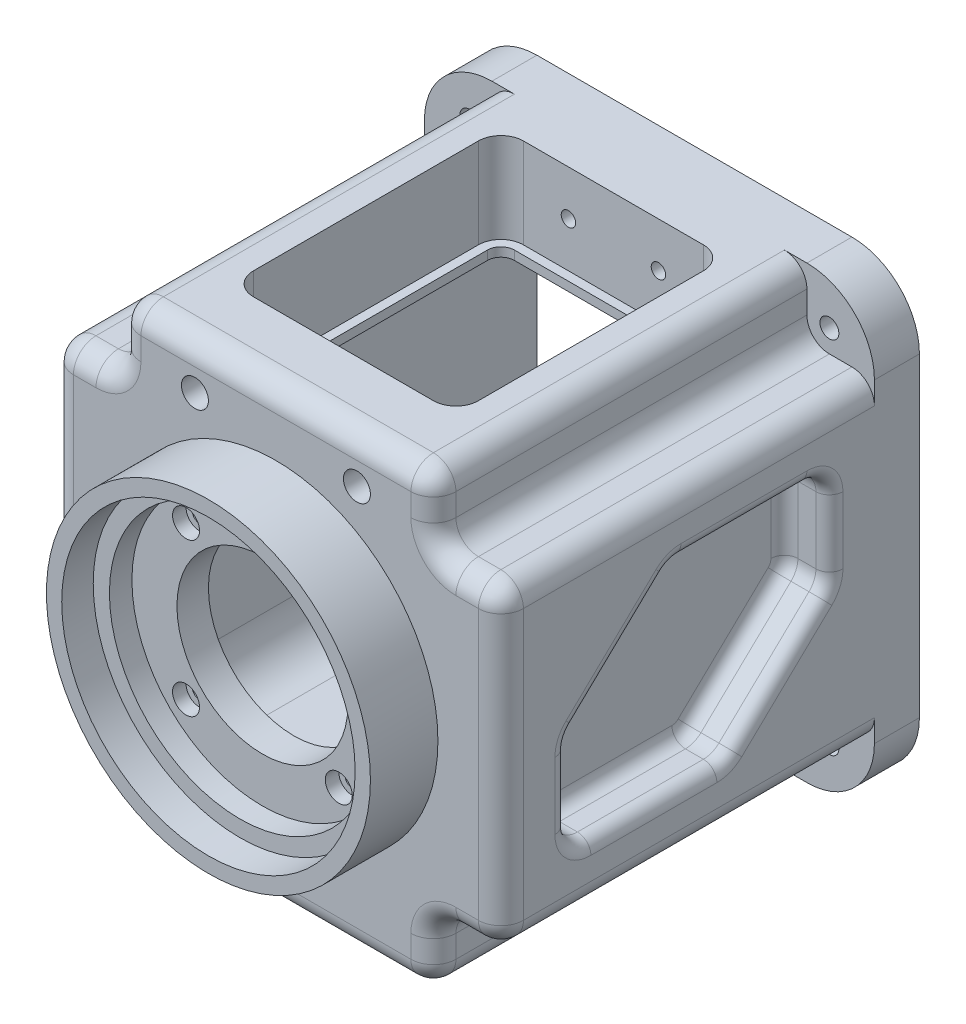
SolidWorks part; units mm, degrees
ref_plane "前视基准面" through (0, 0, 0) normal (0, 0, 1) x (1, 0, 0)
ref_plane "上视基准面" through (0, 0, 0) normal (0, 1, 0) x (1, 0, 0)
ref_plane "右视基准面" through (0, 0, 0) normal (1, 0, 0) x (0, 0, -1)
sketch "草图1" plane through (0, 0, 0) normal (0, 0, 1) x (1, 0, 0)
  line L1 (-50, 50) -> (50, 50)
  line L2 (-50, 50) -> (-50, -50)
  line L3 (-50, -50) -> (50, -50)
  line L4 (50, 50) -> (50, -50)
  line L5 (0, -50) -> (0, 50) construction
  line L6 (-50, 0) -> (50, 0) construction
  point P0 (0, 0)
  dimension "D1" = 100
  dimension "D2" = 100
extrude "凸台-拉伸1" add sketch "草图1" along normal blind 93
fillet "圆角1" radius 15 4 edges at (-50, -50, 46.5) (50, -50, 46.5) (50, 50, 46.5) (-50, 50, 46.5)
sketch "草图2" plane through (0, 0, 93) normal (0, 0, 1) x (1, 0, 0)
  line L0 (35, 50) -> (-35, 50) construction
  line L1 (-35, 50) -> (-50, 50)
  line L2 (-35, 50) -> (-35, 40)
  line L3 (-40, 35) -> (-50, 35)
  line L4 (-50, 50) -> (-50, 35)
  line L5 (-50, 35) -> (-50, -35) construction
  line L6 (50, 35) -> (40, 35)
  line L7 (50, 35) -> (50, 50)
  line L8 (50, 50) -> (35, 50)
  line L9 (35, 40) -> (35, 50)
  line L10 (35, -50) -> (35, -40)
  line L11 (35, -50) -> (50, -50)
  line L12 (50, -50) -> (50, -35)
  line L13 (40, -35) -> (50, -35)
  line L14 (-50, -35) -> (-40, -35)
  line L15 (-50, -35) -> (-50, -50)
  line L16 (-50, -50) -> (-35, -50)
  line L17 (-35, -40) -> (-35, -50)
  arc A0 (-35, 40) -> (-40, 35) centre (-40, 40) cw
  arc A1 (40, 35) -> (35, 40) centre (40, 40) cw
  arc A2 (35, -40) -> (40, -35) centre (40, -40) cw
  arc A3 (-40, -35) -> (-35, -40) centre (-40, -40) cw
  point P31 (0, 0)
  dimension "D3" = 5
  dimension "D1" = 15
  dimension "D2" = 15
  dimension "D4" = 4
extrude "切除-拉伸1" cut sketch "草图2" against normal offset from surface (83 mm away) 10 up to face at (0, 0, 0)
sketch "草图3" plane through (0, -50, 0) normal (0, -1, 0) x (1, 0, 0)
  line L1 (0, 46.5) -> (-87.2172, 46.5) construction
  line L4 (0, 46.5) -> (0, 0) construction
  line L5 (-35, 93) -> (35, 93) construction
  line L6 (-35, 0) -> (35, 0) construction
  circle A0 centre (0, 46.5) radius 25
  circle A1 centre (0, 46.5) radius 15
  dimension "D1" = 50
  dimension "D2" = 30
extrude "切除-拉伸2" cut sketch "草图3" against normal blind 7
sketch "草图4" plane through (0, -43, 0) normal (0, -1, 0) x (1, 0, 0)
  circle A0 centre (0, 46.5) radius 16
  circle A1 centre (0, 46.5) radius 24
  dimension "D1" = 48
  dimension "D2" = 32
extrude "切除-拉伸3" cut sketch "草图4" against normal blind 3
chamfer "倒角1" distance 1 angle 45 2 edges at (0, -50, 31.5) (0, -50, 21.5)
sketch "草图5" plane through (0, 0, 93) normal (0, 0, 1) x (1, 0, 0)
  circle A0 centre (0, 0) radius 36
  dimension "D1" = 72
extrude "凸台-拉伸2" add sketch "草图5" along normal blind 15
sketch "草图6" plane through (0, 0, 108) normal (0, 0, 1) x (1, 0, 0)
  circle A0 centre (0, 0) radius 32.6
  dimension "D2" = 65.2
extrude "切除-拉伸4" cut sketch "草图6" against normal blind 7
sketch "草图7" plane through (0, 0, 101) normal (0, 0, 1) x (1, 0, 0)
  circle A0 centre (0, 0) radius 29
  dimension "D1" = 58
extrude "切除-拉伸5" cut sketch "草图7" against normal blind 5
sketch "草图8" plane through (0, 0, 96) normal (0, 0, 1) x (1, 0, 0)
  line L0 (0, 0) -> (-51.1806, 0) construction
  line L1 (-16.9706, 16.9706) -> (0, 0) construction
  circle A0 centre (0, 0) radius 19
  circle A1 centre (-16.9706, 16.9706) radius 1.6
  circle A2 centre (16.9706, 16.9706) radius 1.6
  circle A3 centre (16.9706, -16.9706) radius 1.6
  circle A4 centre (-16.9706, -16.9706) radius 1.6
  point P15 (0, 0)
  dimension "D1" = 38
  dimension "D3" = 3.2
  dimension "D2" = 45
  dimension "D4" = 24
  dimension "D5" = 4
extrude "切除-拉伸6" cut sketch "草图8" against normal through all
sketch "草图9" plane through (0, 0, 96) normal (0, 0, 1) x (1, 0, 0)
  circle A0 centre (-16.9706, 16.9706) radius 3
  circle A1 centre (16.9706, 16.9706) radius 3
  circle A2 centre (-16.9706, -16.9706) radius 3
  circle A3 centre (16.9706, -16.9706) radius 3
  dimension "D1" = 6
extrude "切除-拉伸7" cut sketch "草图9" against normal blind 3
sketch "草图10" plane through (0, 0, 96) normal (0, 0, 1) x (1, 0, 0)
  line L1 (-19, 0) -> (-28, 0)
  line L2 (-19, 0) -> (-19, -7)
  line L3 (-19, -7) -> (-28, -7)
  line L4 (-28, 0) -> (-28, -7)
  circle A0 centre (0, 0) radius 19 construction
  dimension "D1" = 7
  dimension "D2" = 9
extrude "凸台-拉伸4" [suppressed] add sketch "草图10" along normal blind 5
fillet "圆角2" [suppressed] radius 5
sketch "草图11" plane through (0, 0, 0) normal (0, 0, -1) x (-1, 0, 0)
  line L0 (35, -50) -> (-35, -50) construction
  line L1 (-25, 28) -> (25, 28)
  line L2 (-35, 18) -> (-35, -27)
  line L3 (-25, -37) -> (25, -37)
  line L4 (35, 18) -> (35, -27)
  line L5 (0, -37) -> (0, 28) construction
  line L6 (-35, -4.5) -> (35, -4.5) construction
  arc A0 (25, 28) -> (35, 18) centre (25, 18) cw
  arc A1 (-25, 28) -> (-35, 18) centre (-25, 18) ccw
  arc A2 (-35, -27) -> (-25, -37) centre (-25, -27) ccw
  arc A3 (25, -37) -> (35, -27) centre (25, -27) ccw
  point P0 (0, 0)
  point P6 (35, 28)
  point P10 (-35, 28)
  point P13 (-35, -37)
  dimension "D3" = 10
  dimension "D1" = 65
  dimension "D2" = 70
  dimension "D4" = 13
extrude "切除-拉伸8" cut sketch "草图11" against normal blind 88
sketch "草图12" plane through (0, 0, 88) normal (0, 0, -1) x (-1, 0, 0)
  line L1 (-21.1, 21.1) -> (21.1, 21.1)
  line L2 (-21.1, 21.1) -> (-21.1, -21.1)
  line L3 (-21.1, -21.1) -> (21.1, -21.1)
  line L4 (21.1, 21.1) -> (21.1, -21.1)
  line L5 (0, -21.1) -> (0, 21.1) construction
  line L6 (-21.1, 0) -> (21.1, 0) construction
  point P0 (0, 0)
  dimension "D1" = 42.2
  dimension "D2" = 42.2
extrude "切除-拉伸9" cut sketch "草图12" against normal blind 1
fillet "圆角3" radius 5 24 edges at (-45, -35, 93) (-36.4645, -36.4645, 93) (-35, -45, 93) (0, -50, 93) (36.4645, -36.4645, 93) (35, -45, 93) (45, -35, 93) (50, 0, 93) (45, 35, 93) (36.4645, 36.4645, 93) (35, 45, 93) (0, 50, 93) (-35, 45, 93) (-36.4645, 36.4645, 93) (-45, 35, 93) (-50, 0, 93) (35, 50, 51.5) (50, 35, 51.5) (50, -35, 51.5) (35, -50, 51.5) (-35, -50, 51.5) (-50, -35, 51.5) (-50, 35, 51.5) (-35, 50, 51.5)
sketch "草图13" plane through (0, 50, 0) normal (0, 1, 0) x (1, 0, 0)
  line L0 (35, 0) -> (-35, 0) construction
  line L1 (-20, -20) -> (20, -20)
  line L2 (-23, -23) -> (-23, -73)
  line L3 (-20, -76) -> (20, -76)
  line L4 (23, -23) -> (23, -73)
  line L5 (0, -76) -> (0, -20) construction
  line L6 (-23, -48) -> (23, -48) construction
  arc A0 (20, -20) -> (23, -23) centre (20, -23) cw
  arc A1 (-20, -20) -> (-23, -23) centre (-20, -23) ccw
  arc A2 (-23, -73) -> (-20, -76) centre (-20, -73) ccw
  arc A3 (20, -76) -> (23, -73) centre (20, -73) ccw
  point P0 (0, -48)
  point P8 (23, -20)
  point P12 (-23, -20)
  point P15 (-23, -76)
  dimension "D4" = 3
  dimension "D1" = 56
  dimension "D2" = 46
  dimension "D3" = 20
extrude "切除-拉伸10" cut sketch "草图13" against normal up to next
sketch "草图14" plane through (0, 50, 0) normal (0, 1, 0) x (1, 0, 0)
  line L0 (30, -88) -> (30, -10) construction
  line L1 (-20, -18) -> (20, -18)
  line L2 (-25, -23) -> (-25, -73)
  line L3 (-20, -78) -> (20, -78)
  line L4 (25, -23) -> (25, -73)
  line L5 (0, -78) -> (0, -18) construction
  line L6 (-25, -48) -> (25, -48) construction
  line L7 (-30, -10) -> (-30, -88) construction
  line L8 (20, -20) -> (-20, -20) construction
  line L9 (-20, -76) -> (20, -76) construction
  arc A0 (20, -78) -> (25, -73) centre (20, -73) ccw
  arc A1 (-25, -73) -> (-20, -78) centre (-20, -73) ccw
  arc A2 (20, -18) -> (25, -23) centre (20, -23) cw
  arc A3 (-20, -18) -> (-25, -23) centre (-20, -23) ccw
  point P0 (0, -48)
  dimension "D2" = 5
  dimension "D1" = 60
  dimension "D3" = 50
extrude "切除-拉伸11" cut sketch "草图14" against normal blind 20
sketch "草图15" plane through (-50, 0, 0) normal (-1, 0, 0) x (0, 0, 1)
  line L0 (78, -22) -> (78, 0)
  line L1 (78, 0) -> (55, 22)
  line L2 (55, 22) -> (20, 22)
  line L3 (20, 22) -> (20, 0)
  line L4 (20, 0) -> (43, -22)
  line L5 (43, -22) -> (78, -22)
  line L6 (0, 35) -> (0, -35) construction
  line L7 (93, 30) -> (93, -30) construction
  line L8 (78, 0) -> (20, 0) construction
  line L9 (88, 30) -> (10, 30) construction
  line L10 (10, -30) -> (88, -30) construction
  dimension "D1" = 20
  dimension "D2" = 35
  dimension "D3" = 15
  dimension "D4" = 22
extrude "切除-拉伸12" cut sketch "草图15" against normal blind 10
mirror "镜向1" about plane through (0, 0, 0) normal (1, 0, 0) of "切除-拉伸12"
fillet "圆角4" radius 5 12 edges at (-45, 22, 20) (-45, 0, 20) (-45, -22, 43) (-45, -22, 78) (-45, 0, 78) (-45, 22, 55) (45, 0, 78) (45, 22, 55) (45, 22, 20) (45, 0, 20) (45, -22, 43) (45, -22, 78)
fillet "圆角5" radius 3 48 edges at (-40, 21.6404, 54.8557) (-40, 11.045, 66.453) (-40, -0.1718, 77.5979) (-40, -20.5355, 76.5355) (-40, -22, 59.0031) (-40, -21.6404, 43.1443) (-40, -11.045, 31.547) (-40, 0.1718, 20.4021) (-40, 9.5682, 20) (-40, 20.5355, 21.4645) (-50, 21.6404, 54.8557) (-50, -0.1718, 77.5979) (-50, -9.5682, 78) (-50, -20.5355, 76.5355) (-50, -21.6404, 43.1443) (-50, 0.1718, 20.4021) (-50, 20.5355, 21.4645) (-50, 9.5682, 20) (-50, -11.045, 31.547) (-50, -22, 59.0031) (-40, -9.5682, 78) (-50, 11.045, 66.453) (-40, 22, 38.9969) (-50, 22, 38.9969) (40, -21.6404, 43.1443) (40, -11.045, 31.547) (40, 0.1718, 20.4021) (40, 9.5682, 20) (40, 20.5355, 21.4645) (40, 22, 38.9969) (40, 21.6404, 54.8557) (40, 11.045, 66.453) (40, -0.1718, 77.5979) (40, -9.5682, 78) (40, -20.5355, 76.5355) (50, -21.6404, 43.1443) (50, -11.045, 31.547) (50, 0.1718, 20.4021) (50, 9.5682, 20) (50, 20.5355, 21.4645) (50, 22, 38.9969) (50, 21.6404, 54.8557) (50, 11.045, 66.453) (50, -0.1718, 77.5979) (50, -9.5682, 78) (50, -20.5355, 76.5355) (40, -22, 59.0031) (50, -22, 59.0031)
sketch "草图16" plane through (0, 0, 0) normal (0, 0, -1) x (-1, 0, 0)
  line L0 (0, 0) -> (-72.8216, 0) construction
  line L1 (0, 0) -> (0, 55.6769) construction
  circle A0 centre (-40, 40) radius 2.1
  circle A1 centre (40, 40) radius 2.1
  circle A2 centre (40, -40) radius 2.1
  circle A3 centre (-40, -40) radius 2.1
  point P15 (0, 0)
  dimension "D3" = 4.2
  dimension "D1" = 40
  dimension "D2" = 40
  dimension "D4" = 4
extrude "切除-拉伸13" cut sketch "草图16" against normal through all
sketch "草图17" plane through (0, -40, 0) normal (0, -1, 0) x (1, 0, 0)
  line L0 (19, 52.5) -> (19, 40.5) construction
  line L3 (0, 0) -> (0, 66) construction
  line L4 (22.2, 52.5) -> (22.2, 40.5)
  line L7 (19, 46.5) -> (-28.2912, 46.5) construction
  line L8 (15.8, 52.5) -> (15.8, 40.5)
  arc A4 (22.2, 52.5) -> (15.8, 52.5) centre (19, 52.5) ccw
  arc A5 (15.8, 40.5) -> (22.2, 40.5) centre (19, 40.5) ccw
  circle A7 centre (0, 46.5) radius 8.4626 construction
  point P2 (19, 46.5)
  dimension "D3" = 3.2
  dimension "D1" = 19
  dimension "D2" = 12
extrude "切除-拉伸14" cut sketch "草图17" against normal up to next
sketch "草图18" plane through (0, 0, 0) normal (0, 0, -1) x (-1, 0, 0)
  line L0 (0, 0) -> (0, 55.6154) construction
  line L1 (-35, 50) -> (35, 50) construction
  circle A0 centre (-10, 40) radius 1.6
  circle A1 centre (10, 40) radius 1.6
  dimension "D3" = 3.2
  dimension "D1" = 10
  dimension "D2" = 10
extrude "切除-拉伸15" cut sketch "草图18" against normal up to next
sketch "草图19" plane through (0, 0, 0) normal (0, 0, -1) x (-1, 0, 0)
  circle A0 centre (-10, 40) radius 3
  circle A1 centre (10, 40) radius 3
  dimension "D1" = 6
extrude "切除-拉伸16" cut sketch "草图19" against normal offset from surface (10 mm away) 8 up to face at (8.4, 40, 18)
sketch "草图20" plane through (0, 0, 78) normal (0, 0, -1) x (-1, 0, 0)
  line L0 (0, 0) -> (0, 55.0796) construction
  line L1 (20, 50) -> (-20, 50) construction
  circle A0 centre (-18, 40) radius 1.6
  circle A1 centre (18, 40) radius 1.6
  dimension "D1" = 3.2
  dimension "D2" = 36
  dimension "D3" = 10
extrude "切除-拉伸17" cut sketch "草图20" against normal through all
sketch "草图21" plane through (0, 0, 93) normal (0, 0, 1) x (1, 0, 0)
  circle A0 centre (-18, 40) radius 3
  circle A1 centre (18, 40) radius 3
  dimension "D1" = 6
extrude "切除-拉伸18" cut sketch "草图21" against normal blind 8
